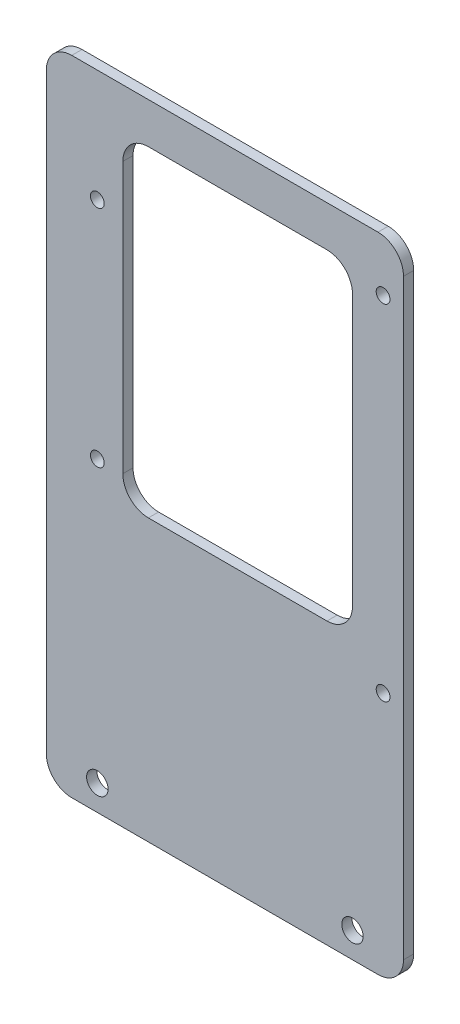
SolidWorks part; units mm, degrees
material "E-玻璃纤维"
ref_plane "前视基准面" through (0, 0, 0) normal (0, 0, 1) x (1, 0, 0)
ref_plane "上视基准面" through (0, 0, 0) normal (0, 1, 0) x (1, 0, 0)
ref_plane "右视基准面" through (0, 0, 0) normal (1, 0, 0) x (0, 0, -1)
sketch "草图1" plane through (0, 0, 0) normal (0, 0, 1) x (1, 0, 0)
  line L1 (-35, -63) -> (35, -63)
  line L2 (-35, -63) -> (-35, 63)
  line L3 (-35, 63) -> (35, 63)
  line L4 (35, -63) -> (35, 63)
  line L5 (-35, -63) -> (35, 63) construction
  line L6 (-35, 63) -> (35, -63) construction
  point P0 (0, 0)
  dimension "D1" = 126
  dimension "D2" = 70
extrude "凸台-拉伸1" add sketch "草图1" along normal blind 2
fillet "圆角1" radius 5 4 edges at (35, -63, 1) (-35, -63, 1) (35, 63, 1) (-35, 63, 1)
sketch "草图2" plane through (0, 0, 2) normal (0, 0, 1) x (1, 0, 0)
  line L0 (0, -58.9537) -> (0, 68.8899) construction
  line L1 (-30, -63) -> (30, -63) construction
  circle A0 centre (-25, -58) radius 2.1
  circle A1 centre (25, -58) radius 2.1
  circle A2 centre (-25, -3) radius 1.35
  circle A3 centre (-25, 41) radius 1.35
  circle A4 centre (31, 52.75) radius 1.35
  circle A5 centre (31, -14.75) radius 1.35
  dimension "D1" = 50
  dimension "D5" = 4.2
  dimension "D6" = 2.7
  dimension "D7" = 2.7
  dimension "D8" = 67.5
  dimension "D10" = 2.7
  dimension "D11" = 2.7
  dimension "D2" = 55
  dimension "D3" = 44
  dimension "D4" = 5
  dimension "D9" = 56
  dimension "D12" = 11.75
extrude "切除-拉伸1" cut sketch "草图2" against normal through all
sketch "草图3" plane through (0, 0, 2) normal (0, 0, 1) x (1, 0, 0)
  line L0 (30, 63) -> (-30, 63) construction
  line L1 (-20, -8) -> (25, -8)
  line L2 (-20, -8) -> (-20, 55)
  line L3 (-20, 55) -> (25, 55)
  line L4 (25, -8) -> (25, 55)
  line L5 (-20, -8) -> (25, 55) construction
  line L6 (-20, 55) -> (25, -8) construction
  line L7 (35, -58) -> (35, 58) construction
  line L8 (-35, 58) -> (-35, -58) construction
  circle A0 centre (25, -58) radius 2.1 construction
  point P0 (2.5, 23.5)
  dimension "D1" = 8
  dimension "D2" = 15
  dimension "10" = 10
  dimension "D3" = 50
extrude "切除-拉伸2" cut sketch "草图3" against normal blind 10
fillet "圆角2" radius 5 4 edges at (25, -8, 1) (-20, 55, 1) (25, 55, 1) (-20, -8, 1)
